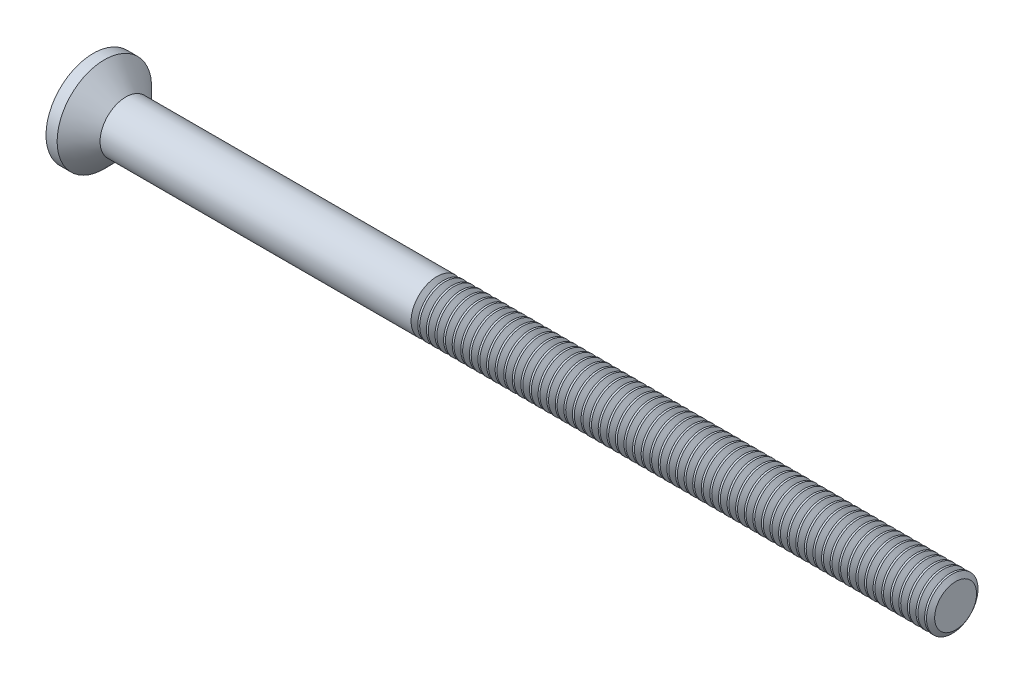
SolidWorks part; units mm, degrees
revolve "Base-Revolve" add sketch "BodySke" angle 360 about L4
sketch "BodySke" plane through (0, 0, 0) normal (0, 0, 1) x (1, 0, 0)
  line L0 (0, 0) -> (50.7277, 0)
  line L1 (50.7277, 0) -> (50.7277, 1.5)
  line L2 (50.7277, 1.5) -> (2.4277, 1.5)
  line L3 (2.4277, 1.5) -> (-7.1953, 11.123) construction
  line L4 (-15.875, 0) -> (82.55, 0) construction
  line L5 (2.4277, -1.5) -> (-7.1953, -11.123) construction
  line L6 (2.9277, 4.675) -> (2.9277, -11.2) construction
  line L7 (20.7277, 8.7375) -> (20.7277, -7.1375) construction
  line L8 (2.4277, 1.5) -> (1.1777, 2.75)
  line L9 (1.1777, 2.75) -> (0.53, 2.75)
  arc A0 (0, 0) -> (0.53, 2.75) centre (7.4, 0) cw
  arc A1 (0.7277, 3.2) -> (0, 0) centre (7.4, 0) ccw construction
  dimension "Crown_rad" = 7.4
  dimension "Diameter" = 3
  dimension "Advance" = 0.5
  dimension "Thread_nom" = 30
  dimension "Head_ang" = 90
  dimension "D3" = 6.4
  dimension "Side_ht" = 1.7
  dimension "D4" = 0.7277
  dimension "Length" = 50
  dimension "Head_dia" = 5.5
cosmetic thread "ThreadCosmetic" [suppressed] parameters "Thread_length"=30, "Thread_minor"=2.439
ref_plane "Plane1" through (0, 0, 0) normal (0, 0, 1) x (1, 0, 0)
ref_plane "Plane2" through (0, 0, 0) normal (0, 1, 0) x (1, 0, 0)
ref_plane "Plane3" through (0, 0, 0) normal (1, 0, 0) x (0, 0, -1)
sketch "Sketch2" plane through (0, 0, 0) normal (1, 0, 0) x (0, 0, -1)
  line L0 (2.75, -0.5) -> (-2.75, -0.5)
  line L1 (2.75, -0.5) -> (2.75, 0.5)
  line L2 (-2.75, 0.5) -> (2.75, 0.5)
  line L3 (-2.75, 0.5) -> (-2.75, -0.5)
  dimension "D1" = 5.5
  dimension "Slot_width" = 1
  dimension "D3" = 2.75
  dimension "D4" = 0.5
extrude "Slot" [suppressed] cut sketch "Sketch2" along normal blind 1.5
sketch "Sketch3" plane through (0, 0, 0) normal (1, 0, 0) x (0, 0, -1)
  line L0 (0.415, -1.72) -> (-0.415, -1.72)
  line L1 (0.415, -1.72) -> (0.415, 1.72)
  line L2 (-0.415, 1.72) -> (0.415, 1.72)
  line L3 (-0.415, 1.72) -> (-0.415, -1.72)
  dimension "Cross_width" = 0.83
  dimension "D1" = 0.415
  dimension "Cross_dia" = 3.44
  dimension "D2" = 1.72
ref_plane "Plane4" through (2.33, 0, 0) normal (1, 0, 0) x (0, 0, -1)
sketch "Sketch4" plane through (2.33, 0, 0) normal (1, 0, 0) x (0, 0, -1)
  line L0 (0.2075, -0.2075) -> (-0.2075, -0.2075)
  line L1 (0.2075, -0.2075) -> (0.2075, 0.2075)
  line L2 (-0.2075, 0.2075) -> (0.2075, 0.2075)
  line L3 (-0.2075, 0.2075) -> (-0.2075, -0.2075)
  dimension "D1" = 0.415
  dimension "D2" = 0.415
  dimension "D3" = 0.2075
  dimension "D4" = 0.2075
loft "Cross" cut profiles "Sketch3", "Sketch4"
pattern_circular "CirPattern1" count 2 every 90 about axis through (0, 0, 0) along (1, 0, 0) of "Cross"
sketch "ThdSchSke" plane through (0, 0, 0) normal (0, 0, 1) x (1, 0, 0)
  line L0 (20.7277, -1.2195) -> (20.5313, -1.5)
  line L1 (20.7277, -1.2195) -> (20.9241, -1.5)
  line L2 (20.9241, -1.5) -> (20.9241, -1.875)
  line L3 (-3.175, 0) -> (5.1513, 0) construction
  line L5 (20.9241, -1.875) -> (20.5313, -1.875)
  line L6 (20.5313, -1.875) -> (20.5313, -1.5)
  line L8 (50.7277, -1.5) -> (50.7277, 1.5) construction
  dimension "Diameter" = 3
  dimension "Thread_minor" = 2.439
  dimension "Start" = 30
revolve "ThreadSchematic" cut sketch "ThdSchSke" angle 360 about L3
pattern_linear "ThdSchPat" count 61 spacing 0.5 along (1, 0, 0) of "ThreadSchematic"
equation "\"D1@Sketch2\" = \"Head_dia@BodySke\""
equation "\"D3@Sketch2\" = \"D1@Sketch2\" / 2"
equation "\"D4@Sketch2\" = \"Slot_width@Sketch2\" / 2"
equation "\"D1@Sketch3\" = \"Cross_width@Sketch3\" / 2"
equation "\"D2@Sketch3\" = \"Cross_dia@Sketch3\" / 2"
equation "\"D1@Sketch4\" = \"Cross_width@Sketch3\"*.5"
equation "\"D2@Sketch4\" = \"D1@Sketch4\""
equation "\"D3@Sketch4\" = \"D1@Sketch4\" / 2"
equation "\"D4@Sketch4\" = \"D2@Sketch4\" / 2"
equation "\"Thread_length@ThreadCosmetic\" = ((sgn( (\"Length@BodySke\" - \"Advance@BodySke\" - \"Side_ht@BodySke\" ) - \"Thread_nom@BodySke\" )-1)*( (\"Length@BodySke\" - \"Advance@BodySke\" - \"Side_ht@BodySke\" ) - \"Thread_nom@BodySke\" ))/-2+ \"Thread_nom@BodySke\""
equation "\"Thread_minor@ThdSchSke\" = \"Thread_minor@ThreadCosmetic\""
equation "\"Diameter@ThdSchSke\" = \"Diameter@BodySke\""
equation "\"Overcut@ThdSchSke\" = \"Diameter@BodySke\" * 1.25"
equation "\"Start@ThdSchSke\" =  \"Thread_length@ThreadCosmetic\""
equation "\"Num_threads@ThdSchPat\" = int( \"Thread_length@ThreadCosmetic\" / \"Advance@BodySke\" + 0.999 )  + 1"
equation "\"Advance@ThdSchPat\" = \"Thread_length@ThreadCosmetic\" /  (\"Num_threads@ThdSchPat\" - 1) 'relax it"
